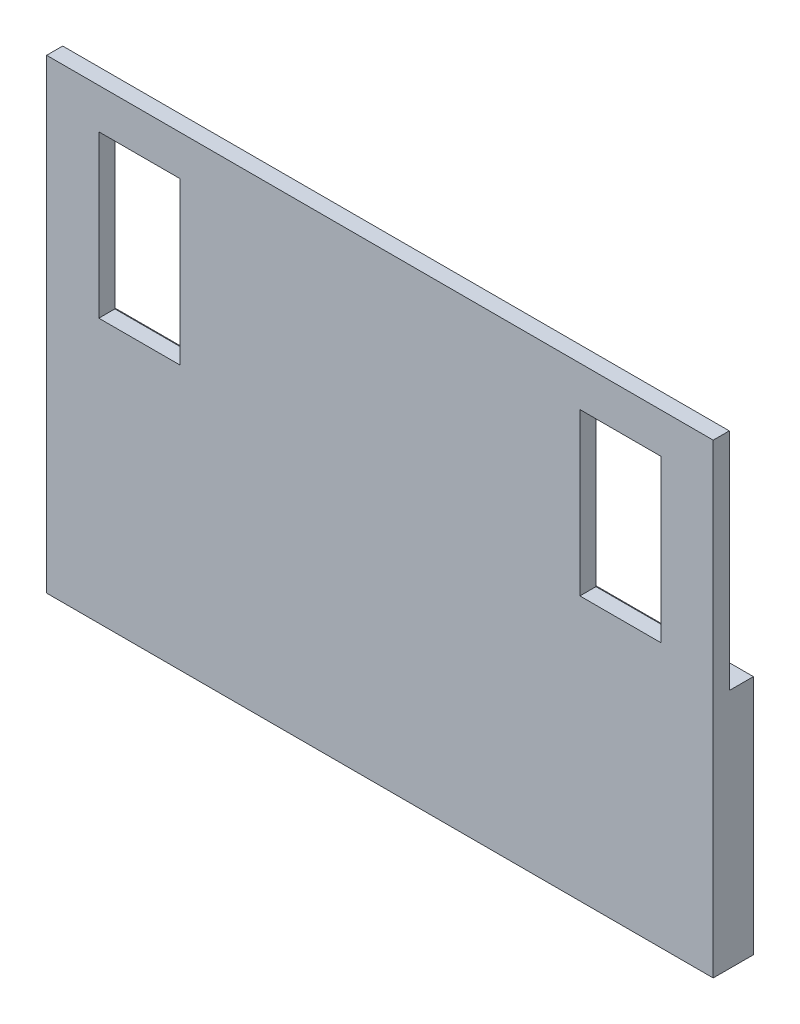
SolidWorks part; units mm, degrees
ref_plane "前视基准面" through (0, 0, 0) normal (0, 0, 1) x (1, 0, 0)
ref_plane "上视基准面" through (0, 0, 0) normal (0, 1, 0) x (1, 0, 0)
ref_plane "右视基准面" through (0, 0, 0) normal (1, 0, 0) x (0, 0, -1)
other "Configuration Table"
sketch "草图1" plane through (0, 0, 0) normal (0, 0, 1) x (1, 0, 0)
  line L0 (-67.65, -48.3307) -> (15.35, -48.3307) construction
  line L1 (-67.65, -20.3307) -> (15.35, -20.3307)
  line L2 (-67.65, -20.3307) -> (-67.65, -78.3307)
  line L3 (-67.65, -78.3307) -> (15.35, -78.3307)
  line L4 (15.35, -20.3307) -> (15.35, -78.3307)
  line L5 (-26.15, -20.3307) -> (-26.15, -78.3307) construction
  line L6 (-1.25, -25.3307) -> (8.85, -25.3307)
  line L7 (-1.25, -25.3307) -> (-1.25, -45.4307)
  line L8 (-1.25, -45.4307) -> (8.85, -45.4307)
  line L9 (8.85, -25.3307) -> (8.85, -45.4307)
  line L10 (-51.05, -45.4307) -> (-61.15, -45.4307)
  line L11 (-61.15, -25.3307) -> (-61.15, -45.4307)
  line L12 (-51.05, -25.3307) -> (-61.15, -25.3307)
  line L13 (-51.05, -25.3307) -> (-51.05, -45.4307)
  line L14 (3.8, -25.3307) -> (3.8, -45.4307) construction
  line L15 (-56.1, -25.3307) -> (-56.1, -45.4307) construction
  dimension "D1" = 30
  dimension "D2" = 58
  dimension "83" = 83
  dimension "D3" = 20.1
  dimension "D4" = 10.1
  dimension "D5" = 5
  dimension "D6" = 6.5
  dimension "D7" = 59.9
extrude "凸台-拉伸1" add sketch "草图1" along normal blind 2
sketch "草图2" plane through (0, 0, 0) normal (0, 0, -1) x (-1, 0, 0)
  line L1 (-15.35, -48.3307) -> (67.65, -48.3307)
  line L2 (-15.35, -48.3307) -> (-15.35, -78.3307)
  line L3 (-15.35, -78.3307) -> (67.65, -78.3307)
  line L4 (67.65, -48.3307) -> (67.65, -78.3307)
extrude "凸台-拉伸2" add sketch "草图2" along normal blind 3
